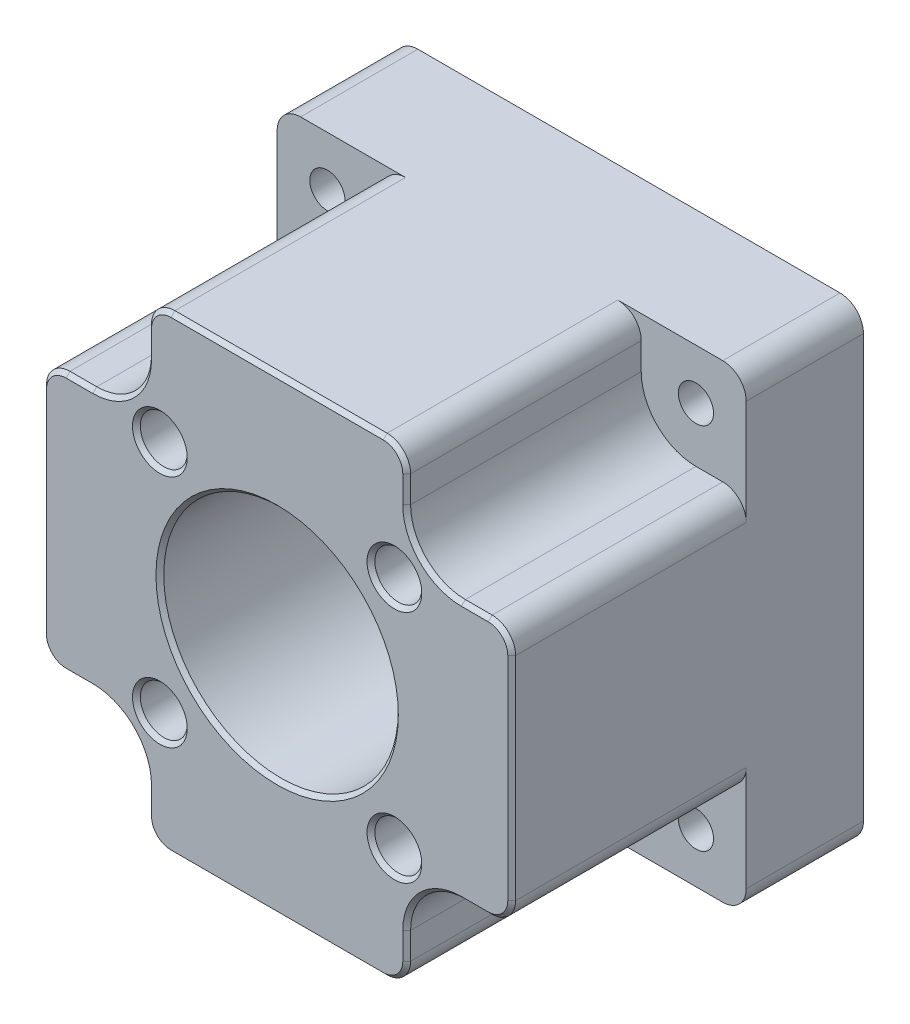
SolidWorks part; units mm, degrees
ref_plane "Front" through (0, 0, 0) normal (0, 0, 1) x (1, 0, 0)
ref_plane "Top" through (0, 0, 0) normal (0, 1, 0) x (1, 0, 0)
ref_plane "Right" through (0, 0, 0) normal (1, 0, 0) x (0, 0, -1)
sketch "Sketch1" plane through (0, 0, 0) normal (0, 0, 1) x (1, 0, 0)
  line L1 (-30, -30) -> (30, -30)
  line L2 (-30, -30) -> (-30, 30)
  line L3 (-30, 30) -> (30, 30)
  line L4 (30, -30) -> (30, 30)
  line L5 (0, 30) -> (0, -30) construction
  line L6 (-30, 0) -> (30, 0) construction
  point P0 (0, 0)
  dimension "D1" = 60
extrude "Boss-Extrude1" add sketch "Sketch1" along normal blind 45
sketch "Sketch3" plane through (0, 0, 45) normal (0, 0, 1) x (1, 0, 0)
  line L0 (0, 23.5712) -> (0, 0) construction
  line L1 (-23.5712, 23.5712) -> (23.5712, 23.5712) construction
  line L2 (-23.5712, 23.5712) -> (-23.5712, -23.5712) construction
  line L3 (-23.5712, -23.5712) -> (23.5712, -23.5712) construction
  line L4 (23.5712, 23.5712) -> (23.5712, -23.5712) construction
  line L5 (0, 0) -> (23.5712, 0) construction
  line L6 (-16.5712, 23.5712) -> (-16.5712, 30)
  line L7 (30, 30) -> (-30, 30) construction
  line L8 (-23.5712, 16.5712) -> (-30, 16.5712)
  line L9 (-30, 30) -> (-30, -30) construction
  line L10 (23.5712, 16.5712) -> (30, 16.5712)
  line L11 (30, -30) -> (30, 30) construction
  line L12 (16.5712, 23.5712) -> (16.5712, 30)
  line L13 (-16.5712, -23.5712) -> (-16.5712, -30)
  line L14 (-30, -30) -> (30, -30) construction
  line L15 (-23.5712, -16.5712) -> (-30, -16.5712)
  line L16 (23.5712, -16.5712) -> (30, -16.5712)
  line L17 (16.5712, -23.5712) -> (16.5712, -30)
  line L18 (-16.5712, 30) -> (-30, 30)
  line L19 (-30, 30) -> (-30, 16.5712)
  line L20 (-30, -16.5712) -> (-30, -30)
  line L21 (-30, -30) -> (-16.5712, -30)
  line L22 (16.5712, -30) -> (30, -30)
  line L23 (30, -30) -> (30, -16.5712)
  circle A0 centre (-23.5712, 23.5712) radius 7 construction
  circle A1 centre (23.5712, 23.5712) radius 7 construction
  circle A2 centre (23.5712, -23.5712) radius 7 construction
  circle A3 centre (-23.5712, -23.5712) radius 7 construction
  arc A4 (-16.5712, 23.5712) -> (-23.5712, 16.5712) centre (-23.5712, 23.5712) cw
  arc A5 (16.5712, 23.5712) -> (23.5712, 16.5712) centre (23.5712, 23.5712) ccw
  arc A6 (23.5712, -16.5712) -> (16.5712, -23.5712) centre (23.5712, -23.5712) ccw
  arc A7 (-23.5712, -16.5712) -> (-16.5712, -23.5712) centre (-23.5712, -23.5712) cw
  line M5 (30, -30) -> (30, 30)
  line M6 (30, 30) -> (-30, 30)
  line M7 (-30, 30) -> (-30, -30)
  line M8 (-30, -30) -> (30, -30)
  dimension "D1" = 47.1424
  dimension "D2" = 14
extrude "Cut-Extrude1" cut sketch "Sketch3" against normal offset from surface (30 mm away) 15 contours A4 L6 L8 M6 M7 | L12 A5 L10 M5 M6 | L16 A6 L17 M8 M5 | A7 L15 L13 M7 M8 up to face at (0, 0, 0)
fillet "Fillet1" radius 3 4 edges at (30, 30, 7.5) (-30, -30, 7.5) (30, -30, 7.5) (-30, 30, 7.5)
sketch "Sketch4" plane through (0, 0, 45) normal (0, 0, 1) x (1, 0, 0)
  circle A0 centre (0, 0) radius 15
  dimension "D1" = 30
extrude "Cut-Extrude2" cut sketch "Sketch4" against normal through all
hole_wizard "M4 Clearance Hole1" positions "3DSketch1" profile "Sketch5" hole size "M4" standard "ANSI Metric" end condition up to next
sketch3d "3DSketch1"
  line L0 (23.5712, 23.5712, 15) -> (23.5712, 23.5712, 45) construction
  line L1 (23.5712, -23.5712, 15) -> (23.5712, -23.5712, 45) construction
  line L2 (-23.5712, -23.5712, 15) -> (-23.5712, -23.5712, 45) construction
  line L3 (-23.5712, 23.5712, 15) -> (-23.5712, 23.5712, 45) construction
  point P0 (-23.5712, 23.5712, 15)
  point P2 (23.5712, 23.5712, 15)
  point P4 (23.5712, -23.5712, 15)
  point P6 (-23.5712, -23.5712, 15)
sketch "Sketch5" plane through (-23.5712, 23.5712, 15) normal (1, 0, 0) x (0, -1, 0)
  line L0 (0, 0) -> (0, 15)
  line L1 (0, 15) -> (2.25, 15)
  line L2 (2.25, 15) -> (2.25, 0)
  line L5 (2.25, 0) -> (0, 0)
  line L11 (0, -6.35) -> (0, 107.95) construction
  dimension "Thru Hole Dia." = 4.5
  dimension "Thru Hole Depth" = 15
sketch "Sketch6" plane through (0, 0, 45) normal (0, 0, 1) x (1, 0, 0)
  line L1 (-15, -15) -> (15, -15) construction
  line L2 (-15, -15) -> (-15, 15) construction
  line L3 (-15, 15) -> (15, 15) construction
  line L4 (15, -15) -> (15, 15) construction
  line L5 (0, 15) -> (0, -15) construction
  line L6 (-15, 0) -> (15, 0) construction
  circle A0 centre (-15, 15) radius 3
  circle A1 centre (-15, -15) radius 3
  circle A2 centre (15, -15) radius 3
  circle A3 centre (15, 15) radius 3
  point P0 (0, 0)
  dimension "D1" = 30
  dimension "D2" = 6
extrude "Cut-Extrude3" cut sketch "Sketch6" against normal blind 20
fillet "Fillet2" radius 3 8 edges at (-30, 16.5712, 30) (-16.5712, 30, 30) (16.5712, 30, 30) (30, 16.5712, 30) (30, -16.5712, 30) (16.5712, -30, 30) (-16.5712, -30, 30) (-30, -16.5712, 30)
chamfer "Chamfer1" distance 0.5 angle 45 29 edges at (-18.6215, 18.6215, 45) (-16.5712, 25.2856, 45) (-15.6925, 29.1213, 45) (0, 30, 45) (15.6925, 29.1213, 45) (16.5712, 25.2856, 45) (18.6215, 18.6215, 45) (25.2856, 16.5712, 45) (29.1213, 15.6925, 45) (30, 0, 45) (29.1213, -15.6925, 45) (25.2856, -16.5712, 45) (18.6215, -18.6215, 45) (16.5712, -25.2856, 45) (15.6925, -29.1213, 45) (0, -30, 45) (-15.6925, -29.1213, 45) (-16.5712, -25.2856, 45) (-18.6215, -18.6215, 45) (-25.2856, -16.5712, 45) (-29.1213, -15.6925, 45) (-30, 0, 45) (-29.1213, 15.6925, 45) (-25.2856, 16.5712, 45) (15, 0, 45) (-12, 15, 45) (-12, -15, 45) (18, -15, 45) (18, 15, 45)
